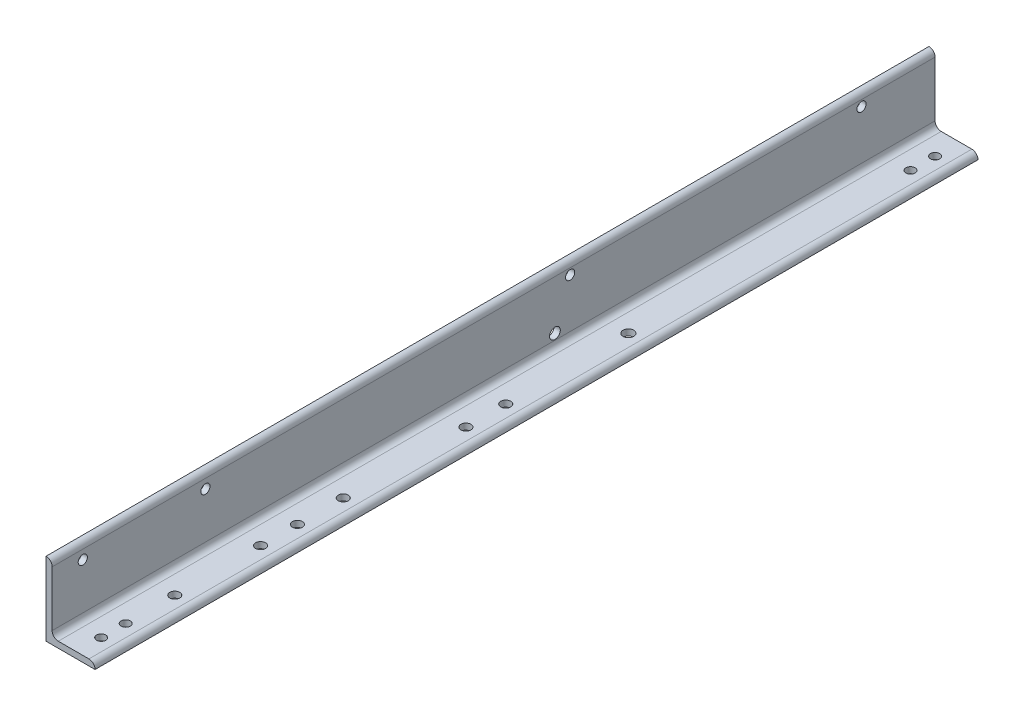
SolidWorks part; units mm, degrees
ref_plane "Front Plane" through (0, 0, 0) normal (0, 0, 1) x (1, 0, 0)
ref_plane "Top Plane" through (0, 0, 0) normal (0, 1, 0) x (1, 0, 0)
ref_plane "Right Plane" through (0, 0, 0) normal (1, 0, 0) x (0, 0, -1)
sketch "Sketch1" plane through (0, 0, 0) normal (0, 0, 1) x (1, 0, 0)
  line L0 (0, 0) -> (0, 152.4)
  line L1 (0, 152.4) -> (0.0051, 152.4)
  line L2 (12.7, 139.7051) -> (12.7, 25.4)
  line L3 (25.4, 12.7) -> (88.9051, 12.7)
  line L4 (101.6, 0.0051) -> (101.6, 0)
  line L5 (101.6, 0) -> (0, 0)
  arc A0 (101.6, 0.0051) -> (88.9051, 12.7) centre (88.9051, 0.0051) ccw
  arc A1 (0.0051, 152.4) -> (12.7, 139.7051) centre (0.0051, 139.7051) cw
  arc A2 (25.4, 12.7) -> (12.7, 25.4) centre (25.4, 25.4) cw
  circle A3 centre (0, 0) radius 12.7 construction
  dimension "D2" = 0.0051
  dimension "Radius_1" = 12.7
  dimension "Radius_2" = 12.7
  dimension "D1" = 12.7
  dimension "V_leg" = 152.4
  dimension "H_leg" = 101.6
  dimension "Thickness" = 12.7
  dimension "Flat_wid" = 0.0051
extrude "Boss-Extrude1" add sketch "Sketch1" along normal mid plane 1828.8
sketch "Sketch3" plane through (0, 12.7, 0) normal (0, 1, 0) x (1, 0, 0)
  line L0 (63.5, -964.9914) -> (63.5, 988.9202) construction
  line L1 (101.6, -914.4) -> (101.6, 914.4) construction
  line L2 (88.9051, -914.4) -> (25.4, -914.4) construction
  line L3 (88.9051, 914.4) -> (25.4, 914.4) construction
  line L4 (63.5, 863.6) -> (63.5, 809.3698) construction
  line L5 (63.5, 812.8) -> (88.9051, 812.8) construction
  line L6 (88.9051, -914.4) -> (88.9051, 914.4) construction
  circle A0 centre (63.5, -863.6) radius 9.525
  circle A1 centre (63.5, 863.6) radius 9.525
  circle A2 centre (63.5, -711.2) radius 10.3187
  circle A3 centre (63.5, -457.2) radius 10.3188
  circle A4 centre (63.5, -108.204) radius 10.3188
  circle A5 centre (63.5, -533.4) radius 10.3187
  circle A6 centre (63.5, -25.654) radius 10.3187
  circle A7 centre (63.5, 228.346) radius 11.1125
  circle A8 centre (63.5, -362.204) radius 10.3188
  circle A9 centre (63.5, 812.8) radius 9.525
  circle A10 centre (63.5, -812.8) radius 9.525
  dimension "D3" = 50.8
  dimension "D4" = 203.2
  dimension "D5" = 254
  dimension "D8" = 254
  dimension "D9" = 20.6375
  dimension "D10" = 888.746
  dimension "D11" = 22.225
  dimension "D7" = 76.2
  dimension "D13" = 50.8
  dimension "D14" = 254
  dimension "D1" = 38.1
  dimension "D2" = 50.8
  dimension "D6" = 552.196
  dimension "D12" = 50.8
extrude "Cut-Extrude2" cut sketch "Sketch3" against normal up to next
sketch "Sketch4" plane through (12.7, 0, 0) normal (1, 0, 0) x (0, 0, -1)
  line L0 (-914.4, 152.4) -> (914.4, 152.4) construction
  line L1 (-914.4, 25.4) -> (-914.4, 139.7051) construction
  line L2 (914.4, 25.4) -> (914.4, 139.7051) construction
  circle A0 centre (-850.9, 120.65) radius 9.525
  circle A1 centre (-596.9, 120.65) radius 9.525
  circle A2 centre (158.496, 127) radius 9.525
  circle A3 centre (762, 127) radius 9.525
  dimension "D1" = 31.75
  dimension "D4" = 254
  dimension "D2" = 31.75
  dimension "D3" = 63.5
  dimension "D5" = 25.4
  dimension "D6" = 755.904
  dimension "D7" = 25.4
  dimension "D8" = 152.4
extrude "Cut-Extrude3" cut sketch "Sketch4" against normal up to next
sketch "Sketch5" plane through (0, 0, 0) normal (-1, 0, 0) x (0, 0, 1)
  line L0 (914.4, 0) -> (-914.4, 0) construction
  line L1 (-914.4, 152.4) -> (-914.4, 0) construction
  circle A0 centre (-127, 38.1) radius 11.1125
  dimension "D1" = 38.1
  dimension "D2" = 787.4
extrude "Cut-Extrude4" cut sketch "Sketch5" against normal through all
equation "\"D3@Sketch3\" = \"D2@Sketch3\""
